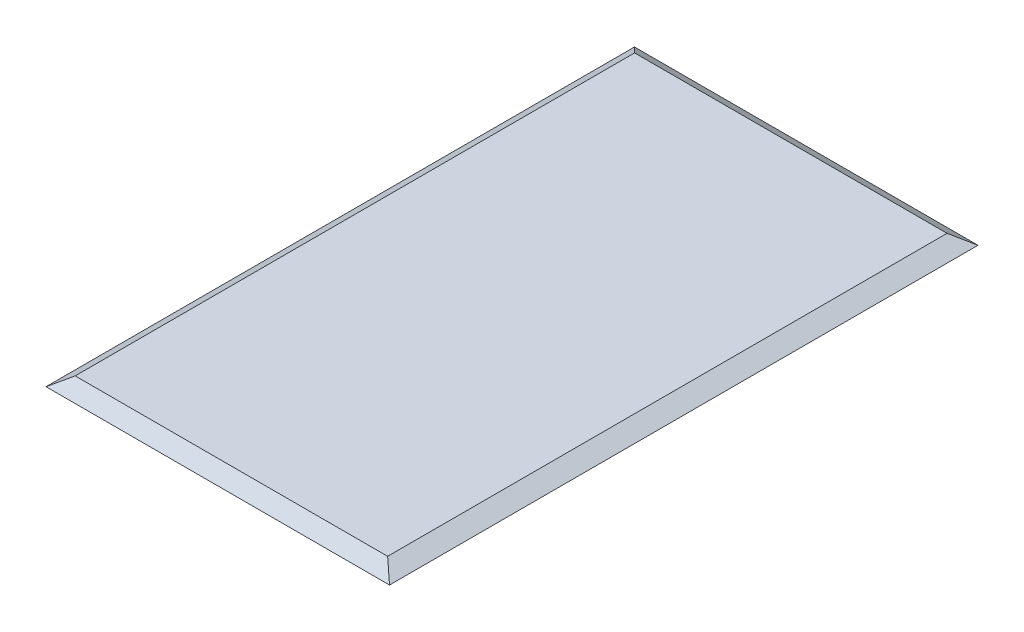
SolidWorks part; units mm, degrees
ref_plane "Спереди" through (0, 0, 0) normal (0, 0, 1) x (1, 0, 0)
ref_plane "Сверху" through (0, 0, 0) normal (0, 1, 0) x (1, 0, 0)
ref_plane "Справа" through (0, 0, 0) normal (1, 0, 0) x (0, 0, -1)
sketch "Эскиз1" plane through (0, 0, 0) normal (0, 1, 0) x (1, 0, 0)
  line L1 (0, 0) -> (3298.0675, 0)
  line L2 (0, 0) -> (0, 5650)
  line L3 (0, 5650) -> (3298.0675, 5650)
  line L4 (3298.0675, 0) -> (3298.0675, 5650)
extrude "Бобышка-Вытянуть1" add sketch "Эскиз1" along normal blind 90
sketch "Эскиз2" plane through (0, 0, 0) normal (0, 0, 1) x (1, 0, 0)
  line L0 (0, 0) -> (140, 90)
  line L1 (0, 90) -> (3298.0675, 90) construction
  line L2 (140, 90) -> (3140, 90)
  line L3 (3140, 90) -> (3298.0675, 0)
  line L4 (3298.0675, 0) -> (0, 0)
extrude "Вырез-Вытянуть1" cut sketch "Эскиз2" against normal through all flip side to cut
sketch "Эскиз3" plane through (0, 0, 0) normal (1, 0, 0) x (0, 0, -1)
  line L0 (0, 0) -> (140, 90)
  line L1 (5650, 90) -> (0, 90) construction
  line L2 (140, 90) -> (5510.896, 90)
  line L3 (5510.896, 90) -> (5650, 0)
  line L4 (5650, 0) -> (0, 0)
extrude "Вырез-Вытянуть4" cut sketch "Эскиз3" along normal through all flip side to cut
sketch "Эскиз4" plane through (0, 0, 0) normal (0, -1, 0) x (1, 0, 0)
  line L1 (140, -140) -> (3140, -140)
  line L2 (140, -140) -> (140, -5530)
  line L3 (140, -5530) -> (3140, -5530)
  line L4 (3140, -140) -> (3140, -5530)
extrude "Вырез-Вытянуть5" cut sketch "Эскиз4" against normal blind 60
